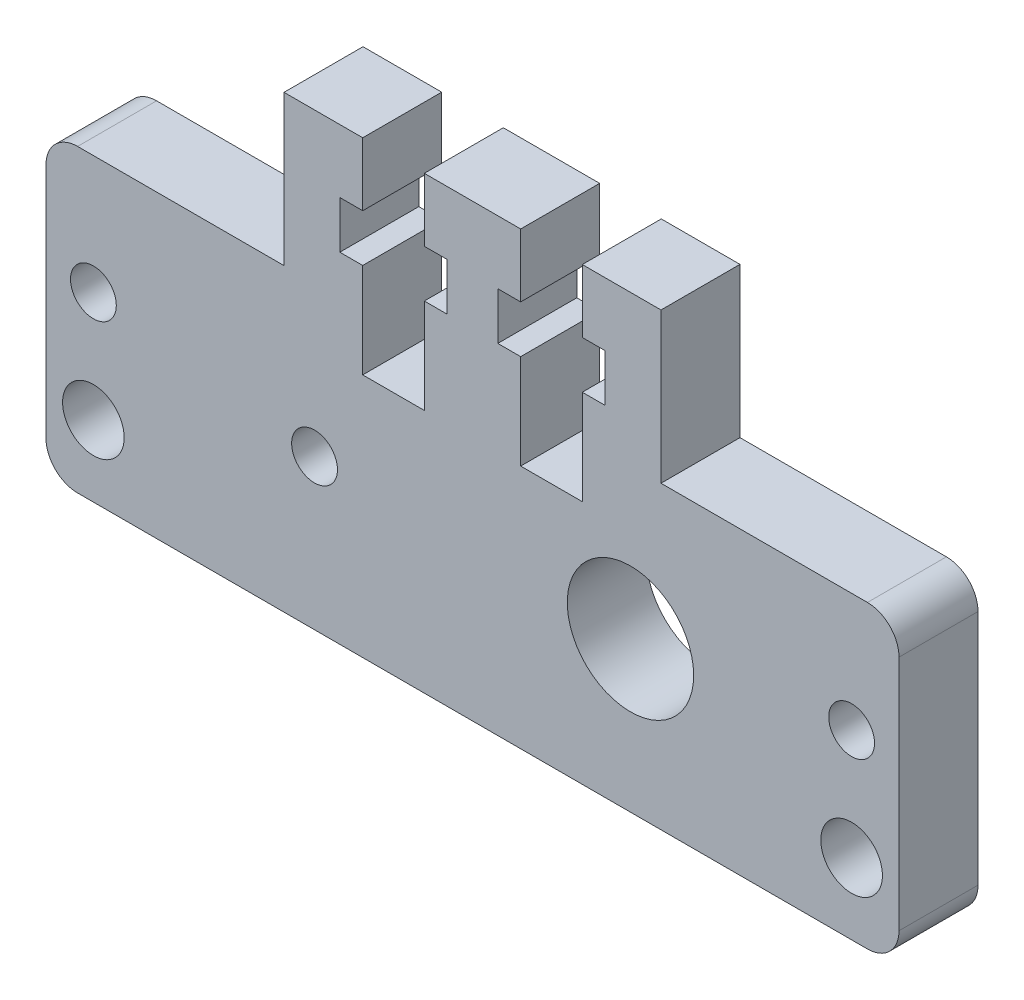
SolidWorks part; units mm, degrees
ref_plane "Front Plane" through (0, 0, 0) normal (0, 0, 1) x (1, 0, 0)
ref_plane "Top Plane" through (0, 0, 0) normal (0, 1, 0) x (1, 0, 0)
ref_plane "Right Plane" through (0, 0, 0) normal (1, 0, 0) x (0, 0, -1)
sketch "Sketch1" plane through (0, 0, -5.5516) normal (0, 0, 1) x (1, 0, 0)
  line L0 (-25.4646, 10.1373) -> (-12.3968, 10.1373)
  line L1 (-27.4646, 8.1373) -> (-27.4646, -6.8627)
  line L2 (26.5354, 8.1373) -> (26.5354, -6.8627)
  line L3 (-25.4646, -8.8627) -> (-10, -8.8627)
  line L4 (-20.7646, 10.1373) -> (-25.9646, 10.1373) construction
  line L5 (-20.7646, -8.8627) -> (-25.9646, -8.8627) construction
  line L6 (-27.4646, -2.971) -> (-27.4646, 4.2457) construction
  line L7 (-12.3968, 10.1373) -> (-12.3968, 19.6373)
  line L8 (-27.4646, 0.6373) -> (26.5354, 0.6373) construction
  line L9 (-24.4646, 10.1373) -> (-24.4646, -8.8627) construction
  line L10 (23.5354, 10.1373) -> (23.5354, -8.8627) construction
  line L27 (6.4854, 19.6373) -> (2.5854, 19.6373) construction
  line L28 (6.4854, 19.6373) -> (6.4854, 15.6373)
  line L40 (4.5354, 19.6373) -> (4.5354, 6.6373) construction
  line L41 (-10, -8.8627) -> (24.5354, -8.8627)
  line L42 (6.4854, 6.6373) -> (2.5854, 6.6373)
  line L44 (6.4854, 12.6373) -> (7.9354, 12.6373)
  line L46 (7.9354, 12.6373) -> (7.9354, 15.6373)
  line L47 (6.4854, 15.6373) -> (7.9354, 15.6373)
  line L48 (6.4854, 12.6373) -> (6.4854, 6.6373)
  line L49 (2.5854, 12.6373) -> (2.5854, 6.6373)
  line L50 (2.5854, 15.6373) -> (1.1354, 15.6373)
  line L51 (1.1354, 12.6373) -> (1.1354, 15.6373)
  line L52 (2.5854, 12.6373) -> (1.1354, 12.6373)
  line L53 (2.5854, 19.6373) -> (2.5854, 15.6373)
  line L54 (-3.5146, 19.6373) -> (-7.4146, 19.6373) construction
  line L55 (-3.5146, 19.6373) -> (-3.5146, 15.6373)
  line L56 (-5.4646, 19.6373) -> (-5.4646, 6.6373) construction
  line L57 (-3.5146, 6.6373) -> (-7.4146, 6.6373)
  line L58 (-3.5146, 12.6373) -> (-2.0646, 12.6373)
  line L59 (-2.0646, 12.6373) -> (-2.0646, 15.6373)
  line L60 (-3.5146, 15.6373) -> (-2.0646, 15.6373)
  line L61 (-3.5146, 12.6373) -> (-3.5146, 6.6373)
  line L62 (-7.4146, 12.6373) -> (-7.4146, 6.6373)
  line L63 (-7.4146, 15.6373) -> (-8.8646, 15.6373)
  line L64 (-8.8646, 12.6373) -> (-8.8646, 15.6373)
  line L65 (-7.4146, 12.6373) -> (-8.8646, 12.6373)
  line L66 (-7.4146, 19.6373) -> (-7.4146, 15.6373)
  line L70 (-0.4646, 80.7583) -> (-0.4646, -22.1769) construction
  line L71 (-12.3968, 19.6373) -> (-7.4146, 19.6373)
  line L73 (-3.5146, 19.6373) -> (2.5854, 19.6373)
  line L75 (6.4854, 19.6373) -> (11.4676, 19.6373)
  line L76 (11.4676, 19.6373) -> (11.4676, 10.1373)
  line L77 (11.4676, 10.1373) -> (24.5354, 10.1373)
  line L79 (26.5354, -7.3627) -> (26.5354, 8.6373) construction
  line L80 (25.0354, 10.1373) -> (19.5354, 10.1373) construction
  arc A0 (24.5354, 10.1373) -> (26.5354, 8.1373) centre (24.5354, 8.1373) cw
  arc A1 (26.5354, -6.8627) -> (24.5354, -8.8627) centre (24.5354, -6.8627) cw
  arc A2 (-27.4646, -6.8627) -> (-25.4646, -8.8627) centre (-25.4646, -6.8627) ccw
  arc A3 (-27.4646, 8.1373) -> (-25.4646, 10.1373) centre (-25.4646, 8.1373) cw
  circle A5 centre (-24.4646, -4.3627) radius 1.95
  circle A6 centre (23.5354, -4.3627) radius 1.95
  circle A12 centre (9.5354, 0.6373) radius 4
  circle A13 centre (-10.4646, 0.6373) radius 1.45
  circle A14 centre (-24.4646, 2.6373) radius 1.45
  circle A15 centre (23.5354, 2.6373) radius 1.45
  arc A16 (25.1969, -3.2494) -> (25.0665, -5.6494) centre (23.5354, -4.3627) ccw construction
  circle A17 centre (9.5354, 0.6373) radius 5 construction
  arc A19 (-25.9958, -5.6494) -> (-26.1261, -3.2494) centre (-24.4646, -4.3627) ccw construction
  point P73 (-0.4646, 80.7583)
  dimension "D1" = 2
  dimension "D2" = 8
  dimension "D3" = 2.9
  dimension "D4" = 2.9
  dimension "D5" = 2.9
  dimension "D19" = 2
  dimension "D20" = 3.9
  dimension "D21" = 27
  dimension "D22" = 3.9
  dimension "D6" = 3.9
  dimension "D7" = 4
  dimension "D8" = 6
  dimension "D9" = 3
  dimension "D10" = 1.45
  dimension "D11" = 3.9
  dimension "D12" = 4
  dimension "D13" = 6
  dimension "D14" = 3
  dimension "D15" = 1.45
  dimension "D16" = 10
  dimension "D17" = 6
  dimension "D18" = 20
  dimension "D23" = 2
extrude "Boss-Extrude1" add sketch "Sketch1" along normal blind 5
